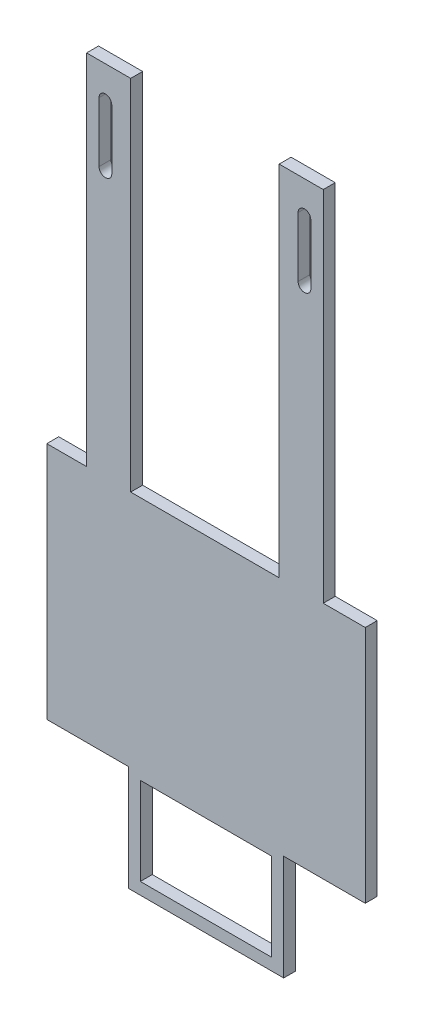
SolidWorks part; units mm, degrees
ref_plane "前视基准面" through (0, 0, 0) normal (0, 0, 1) x (1, 0, 0)
ref_plane "上视基准面" through (0, 0, 0) normal (0, 1, 0) x (1, 0, 0)
ref_plane "右视基准面" through (0, 0, 0) normal (1, 0, 0) x (0, 0, -1)
other "Configuration Table"
sketch "草图1" plane through (0, 0, 0) normal (0, 0, 1) x (1, 0, 0)
  line L0 (12.098, 68.8969) -> (23.1749, 68.8969)
  line L1 (-36.2726, 68.8969) -> (-25.1956, 68.8969)
  line L2 (-46.2726, -21.1031) -> (-46.2726, -81.1031)
  line L3 (-46.2726, -81.1031) -> (-25.7726, -81.1031)
  line L4 (33.7274, -21.1031) -> (33.7274, -81.1031)
  line L6 (-25.1956, 68.8969) -> (-25.1956, -21.1031)
  line L7 (-25.1956, -21.1031) -> (12.098, -21.1031)
  line L8 (12.098, 68.8969) -> (12.098, -21.1031)
  line L9 (-36.2726, 45.7316) -> (23.1749, 45.7316) construction
  line L10 (-6.5488, 45.7316) -> (-6.5488, -21.1031) construction
  line L11 (-31.5488, 45.7316) -> (-31.5488, 60.7316) construction
  line L12 (-33.1488, 45.7316) -> (-33.1488, 60.7316)
  line L13 (-29.9488, 45.7316) -> (-29.9488, 60.7316)
  line L14 (18.4512, 45.7316) -> (18.4512, 60.7316) construction
  line L15 (20.0512, 45.7316) -> (20.0512, 60.7316)
  line L16 (16.8512, 45.7316) -> (16.8512, 60.7316)
  line L17 (-36.2726, 68.8969) -> (-36.2726, -21.1031)
  line L18 (-36.2726, -21.1031) -> (-46.2726, -21.1031)
  line L19 (23.1749, 68.8969) -> (23.1749, -21.1031)
  line L20 (23.1749, -21.1031) -> (33.7274, -21.1031)
  line L21 (-25.7726, -81.1031) -> (-25.7726, -107.6031)
  line L26 (-25.7726, -107.6031) -> (13.2274, -107.6031)
  line L27 (13.2274, -81.1031) -> (13.2274, -107.6031)
  line L29 (-22.7726, -82.6031) -> (-22.7726, -104.6031)
  line L30 (-22.7726, -104.6031) -> (10.2274, -104.6031)
  line L31 (10.2274, -82.6031) -> (10.2274, -104.6031)
  line L32 (-22.7726, -82.6031) -> (10.2274, -82.6031)
  line L36 (13.2274, -81.1031) -> (33.7274, -81.1031)
  arc A0 (-33.1488, 45.7316) -> (-29.9488, 45.7316) centre (-31.5488, 45.7316) ccw
  arc A1 (-29.9488, 60.7316) -> (-33.1488, 60.7316) centre (-31.5488, 60.7316) ccw
  arc A2 (20.0512, 45.7316) -> (16.8512, 45.7316) centre (18.4512, 45.7316) cw
  arc A3 (16.8512, 60.7316) -> (20.0512, 60.7316) centre (18.4512, 60.7316) cw
  point P14 (-31.5488, 53.2316)
  point P22 (18.4512, 53.2316)
  dimension "D5" = 1.6
  dimension "D1" = 80
  dimension "D3" = 60
  dimension "D4" = 25
  dimension "D6" = 15
  dimension "D7" = 10
  dimension "D8" = 90
extrude "凸台-拉伸1" add sketch "草图1" along normal blind 3
